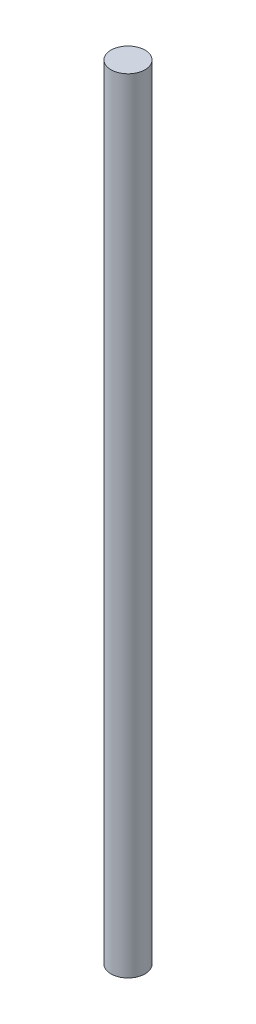
SolidWorks part; units mm, degrees
ref_plane "Front Plane" through (0, 0, 0) normal (0, 0, 1) x (1, 0, 0)
ref_plane "Top Plane" through (0, 0, 0) normal (0, 1, 0) x (1, 0, 0)
ref_plane "Right Plane" through (0, 0, 0) normal (1, 0, 0) x (0, 0, -1)
sketch "Sketch1" plane through (0, 0, 0) normal (0, 1, 0) x (1, 0, 0)
  circle A0 centre (0, 0) radius 3.175
  dimension "D1" = 6.35
extrude "Boss-Extrude1" add sketch "Sketch1" along normal blind 146.05
